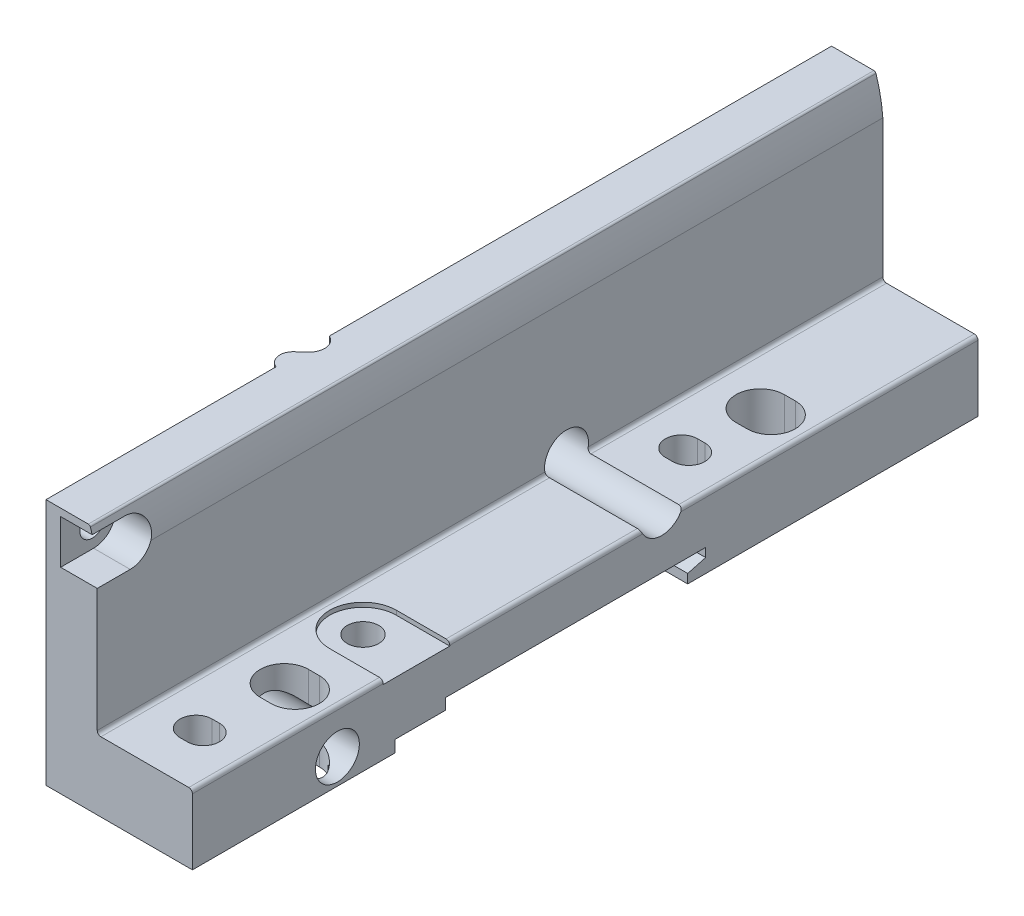
SolidWorks part; units mm, degrees
ref_plane "Front Plane" through (0, 0, 0) normal (0, 0, 1) x (1, 0, 0)
ref_plane "Top Plane" through (0, 0, 0) normal (0, 1, 0) x (1, 0, 0)
ref_plane "Right Plane" through (0, 0, 0) normal (1, 0, 0) x (0, 0, -1)
ref_plane "Plane1" through (0, 0, 0) normal (0, 0, 1) x (1, 0, 0)
sketch "Sketch1" plane through (0, 0, 0) normal (0, 0, 1) x (1, 0, 0)
  line L0 (-5, 1.3) -> (20, 1.3)
  line L1 (20, 1.3) -> (20, 10.3)
  line L2 (19.5, 10.8) -> (7.5, 10.8)
  line L3 (7, 11.3) -> (7, 30.1133)
  line L4 (5.7818, 35.1) -> (-5, 35.1)
  line L5 (-5, 35.1) -> (-5, 1.3)
  arc A0 (20, 10.3) -> (19.5, 10.8) centre (19.5, 10.3) ccw
  arc A1 (7.5, 10.8) -> (7, 11.3) centre (7.5, 11.3) cw
  arc A2 (7, 30.1133) -> (6.067, 34.8929) centre (-12.95, 28.7) ccw
  arc A3 (6.067, 34.8929) -> (5.7818, 35.1) centre (5.7818, 34.8) ccw
extrude "Boss-Extrude1" add sketch "Sketch1" against normal blind 53.65 and the other way blind 53.65
ref_plane "Plane2" through (0, 0, 0) normal (0, 1, 0) x (1, 0, 0)
sketch "Sketch2" plane through (0, 0, 0) normal (0, 1, 0) x (1, 0, 0)
  line L0 (-50, 53.65) -> (-50, -53.65)
  line L1 (-50, -53.65) -> (0, -53.65)
  line L2 (0, -53.65) -> (0, -22.2285)
  line L3 (-0.5795, -19.2353) -> (0.5161, -18.2108)
  line L4 (0, -14.9396) -> (0, 53.65)
  line L5 (0, 53.65) -> (-50, 53.65)
  arc A0 (0, -22.2285) -> (-0.5795, -19.2353) centre (0.65, -20.55) cw
  arc A1 (0.5161, -18.2108) -> (0, -14.9396) centre (-0.85, -16.75) ccw
extrude "Cut-Extrude1" cut sketch "Sketch2" along normal blind 50
ref_plane "Plane3" through (0, 0, 0) normal (1, 0, 0) x (0, 0, -1)
sketch "Sketch3" plane through (0, 0, 0) normal (1, 0, 0) x (0, 0, -1)
  line L0 (-26, 2.9) -> (-26, -8.1744)
  line L1 (-26, -8.1744) -> (14, -7.9637)
  line L2 (14, -7.9637) -> (14, 2.5435)
  line L3 (14, 2.5435) -> (16.45, 3.2)
  line L4 (16.45, 3.2) -> (16.45, 4.4)
  line L5 (16.45, 4.4) -> (-19.05, 4.4)
  line L6 (-19.05, 4.4) -> (-19.05, 2.9)
  line L7 (-19.05, 2.9) -> (-26, 2.9)
extrude "Cut-Extrude2" cut sketch "Sketch3" against normal blind 40 and the other way blind 40
ref_plane "Plane4" through (0, 0, 0) normal (0, 1, 0) x (1, 0, 0)
sketch "Sketch4" plane through (0, 0, 0) normal (0, 1, 0) x (1, 0, 0)
  line L0 (8.8, 16) -> (16.8, 16)
  line L1 (16.8, 16) -> (16.8, 35.5)
  line L2 (16.8, 35.5) -> (8.8, 35.5)
  line L3 (8.8, 35.5) -> (8.8, 16)
extrude "Boss-Extrude2" add sketch "Sketch4" along normal blind 1.5
ref_plane "Plane5" through (0, 0, 0) normal (0, 1, 0) x (1, 0, 0)
sketch "Sketch5" plane through (0, 0, 0) normal (0, 1, 0) x (1, 0, 0)
  line L0 (0, -29.5) -> (0, -49.85)
  line L1 (0, -49.85) -> (16.8, -49.85)
  line L2 (16.8, -49.85) -> (16.8, -29.5)
  line L3 (16.8, -29.5) -> (0, -29.5)
extrude "Boss-Extrude3" add sketch "Sketch5" along normal blind 1.5
ref_plane "Plane6" through (0, 0, 0) normal (0, 1, 0) x (1, 0, 0)
sketch "Sketch6" plane through (0, 0, 0) normal (0, 1, 0) x (1, 0, 0)
  line L0 (13.7, 26.9) -> (15.2, 26.9)
  line L1 (15.2, 33.5) -> (13.7, 33.5)
  arc A0 (13.7, 33.5) -> (13.7, 26.9) centre (13.7, 30.2) ccw
  arc A1 (15.2, 26.9) -> (15.2, 33.5) centre (15.2, 30.2) ccw
extrude "Cut-Extrude3" cut sketch "Sketch6" against normal blind 30 and the other way blind 30
ref_plane "Plane7" through (0, 0, 0) normal (0, 1, 0) x (1, 0, 0)
sketch "Sketch7" plane through (0, 0, 0) normal (0, 1, 0) x (1, 0, 0)
  line L0 (13, 17.95) -> (14, 17.95)
  line L1 (14, 22.35) -> (13, 22.35)
  arc A0 (13, 22.35) -> (13, 17.95) centre (13, 20.15) ccw
  arc A1 (14, 17.95) -> (14, 22.35) centre (14, 20.15) ccw
extrude "Cut-Extrude4" cut sketch "Sketch7" along normal blind 30
ref_plane "Plane8" through (0, 0, 0) normal (0, 1, 0) x (1, 0, 0)
sketch "Sketch8" plane through (0, 0, 0) normal (0, 1, 0) x (1, 0, 0)
  circle A0 centre (12.7, -23.05) radius 2.15
extrude "Cut-Extrude5" cut sketch "Sketch8" along normal blind 30
ref_plane "Plane9" through (0, 0, 0) normal (0, 1, 0) x (1, 0, 0)
sketch "Sketch9" plane through (0, 0, 0) normal (0, 1, 0) x (1, 0, 0)
  line L0 (13.7, -38.1) -> (15.2, -38.1)
  line L1 (15.2, -31.5) -> (13.7, -31.5)
  arc A0 (13.7, -31.5) -> (13.7, -38.1) centre (13.7, -34.8) ccw
  arc A1 (15.2, -38.1) -> (15.2, -31.5) centre (15.2, -34.8) ccw
extrude "Cut-Extrude6" cut sketch "Sketch9" along normal blind 10.8
ref_plane "Plane10" through (0, 0, 0) normal (0, 1, 0) x (1, 0, 0)
sketch "Sketch10" plane through (0, 0, 0) normal (0, 1, 0) x (1, 0, 0)
  line L0 (13, -48.35) -> (14, -48.35)
  line L1 (14, -43.95) -> (13, -43.95)
  arc A0 (13, -43.95) -> (13, -48.35) centre (13, -46.15) ccw
  arc A1 (14, -48.35) -> (14, -43.95) centre (14, -46.15) ccw
extrude "Cut-Extrude7" cut sketch "Sketch10" along normal blind 10.8
ref_plane "Plane11" through (0, 11.8, 0) normal (0, 1, 0) x (1, 0, 0)
sketch "Sketch11" plane through (0, 11.8, 0) normal (0, 1, 0) x (1, 0, 0)
  line L0 (0, 10.45) -> (0, 12.2)
  line L1 (0, 12.2) -> (2, 12.2)
  line L2 (2, 12.2) -> (2, 13.45)
  line L3 (2, 13.45) -> (20, 13.45)
  line L4 (20, 13.45) -> (20, 10.45)
  line L5 (20, 10.45) -> (0, 10.45)
  line L6 (20, 10.45) -> (0, 10.45) construction
revolve "Cut-Revolve1" cut sketch "Sketch11" angle 360 about L6
ref_plane "Plane12" through (0, 4.8, 0) normal (0, 1, 0) x (1, 0, 0)
sketch "Sketch12" plane through (0, 4.8, 0) normal (0, 1, 0) x (1, 0, 0)
  line L0 (0, -33.85) -> (0, -32.1)
  line L1 (0, -32.1) -> (2, -32.1)
  line L2 (2, -32.1) -> (2, -30.85)
  line L3 (2, -30.85) -> (20, -30.85)
  line L4 (20, -30.85) -> (20, -33.85)
  line L5 (20, -33.85) -> (0, -33.85)
  line L6 (20, -33.85) -> (0, -33.85) construction
revolve "Cut-Revolve2" cut sketch "Sketch12" angle 360 about L6
ref_plane "Plane13" through (0, 31.1, 0) normal (0, 1, 0) x (1, 0, 0)
sketch "Sketch13" plane through (0, 31.1, 0) normal (0, 1, 0) x (1, 0, 0)
  line L0 (0, -49.32) -> (0, -47.605)
  line L1 (0, -47.605) -> (20, -47.605)
  line L2 (20, -47.605) -> (20, -49.32)
  line L3 (20, -49.32) -> (0, -49.32)
  line L4 (20, -49.32) -> (0, -49.32) construction
revolve "Cut-Revolve3" cut sketch "Sketch13" angle 360 about L4
ref_plane "Plane14" through (7, 0, 0) normal (1, 0, 0) x (0, 0, -1)
sketch "Sketch14" plane through (7, 0, 0) normal (1, 0, 0) x (0, 0, -1)
  line L0 (-54.15, 28.1) -> (-49.15, 28.1)
  line L1 (-49.15, 34.1) -> (-54.15, 34.1)
  line L2 (-54.15, 34.1) -> (-54.15, 28.1)
  arc A0 (-49.15, 28.1) -> (-49.15, 34.1) centre (-49.15, 31.1) ccw
extrude "Cut-Extrude8" cut sketch "Sketch14" against normal blind 5 and the other way blind 5
ref_plane "Plane15" through (0, 10.8, 0) normal (0, 1, 0) x (1, 0, 0)
sketch "Sketch15" plane through (0, 10.8, 0) normal (0, 1, 0) x (1, 0, 0)
  line L0 (12.7, -27.6) -> (20, -27.6)
  line L1 (20, -27.6) -> (20, -18.5)
  line L2 (20, -18.5) -> (12.7, -18.5)
  arc A0 (12.7, -18.5) -> (12.7, -27.6) centre (12.7, -23.05) ccw
extrude "Cut-Extrude9" cut sketch "Sketch15" against normal blind 0.6
ref_plane "Plane16" through (0, 0, 0) normal (0, 1, 0) x (1, 0, 0)
sketch "Sketch16" plane through (0, 0, 0) normal (0, 1, 0) x (1, 0, 0)
  line L0 (3.65, 13.95) -> (15.65, 13.95)
  line L1 (15.65, 13.95) -> (15.65, 16.45)
  line L2 (15.65, 16.45) -> (3.65, 16.45)
  line L3 (3.65, 16.45) -> (3.65, 13.95)
extrude "Cut-Extrude10" cut sketch "Sketch16" along normal blind 3.5
